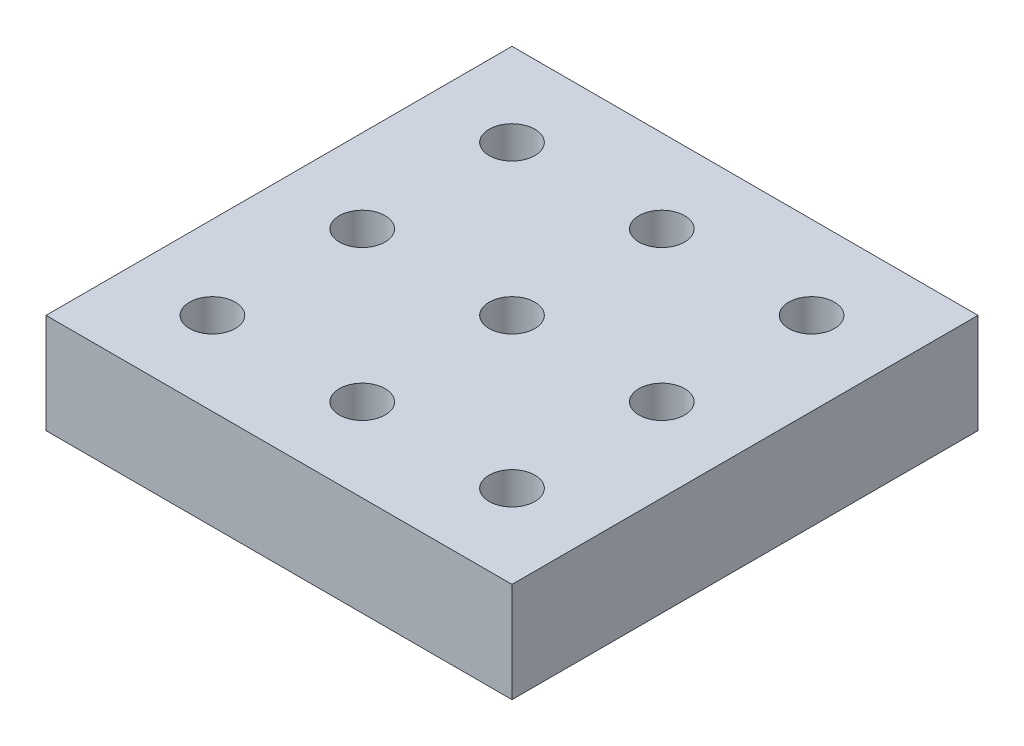
SolidWorks part; units mm, degrees
ref_plane "Front Plane" through (0, 0, 0) normal (0, 0, 1) x (1, 0, 0)
ref_plane "Top Plane" through (0, 0, 0) normal (0, 1, 0) x (1, 0, 0)
ref_plane "Right Plane" through (0, 0, 0) normal (1, 0, 0) x (0, 0, -1)
sketch "Sketch1" plane through (0, 0, 0) normal (0, 1, 0) x (1, 0, 0)
  line L1 (-52.9114, 47.2934) -> (3.0886, 47.2934)
  line L2 (-52.9114, 47.2934) -> (-52.9114, -8.7066)
  line L3 (-52.9114, -8.7066) -> (3.0886, -8.7066)
  line L4 (3.0886, 47.2934) -> (3.0886, -8.7066)
  circle A0 centre (-42.9114, 37.2934) radius 2.75
  circle A1 centre (-24.9114, 37.2934) radius 2.75
  circle A2 centre (-6.9114, 37.2934) radius 2.75
  circle A3 centre (-24.9114, 19.2934) radius 2.75
  circle A4 centre (-6.9114, 19.2934) radius 2.75
  circle A5 centre (-24.9114, 1.2934) radius 2.75
  circle A6 centre (-6.9114, 1.2934) radius 2.75
  circle A7 centre (-42.9114, 19.2934) radius 2.75
  circle A8 centre (-42.9114, 1.2934) radius 2.75
  dimension "D5" = 5.5
  dimension "D3" = 10
  dimension "D1" = 10
  dimension "D2" = 10
  dimension "D4" = 10
extrude "Boss-Extrude2" add sketch "Sketch1" along normal blind 12
